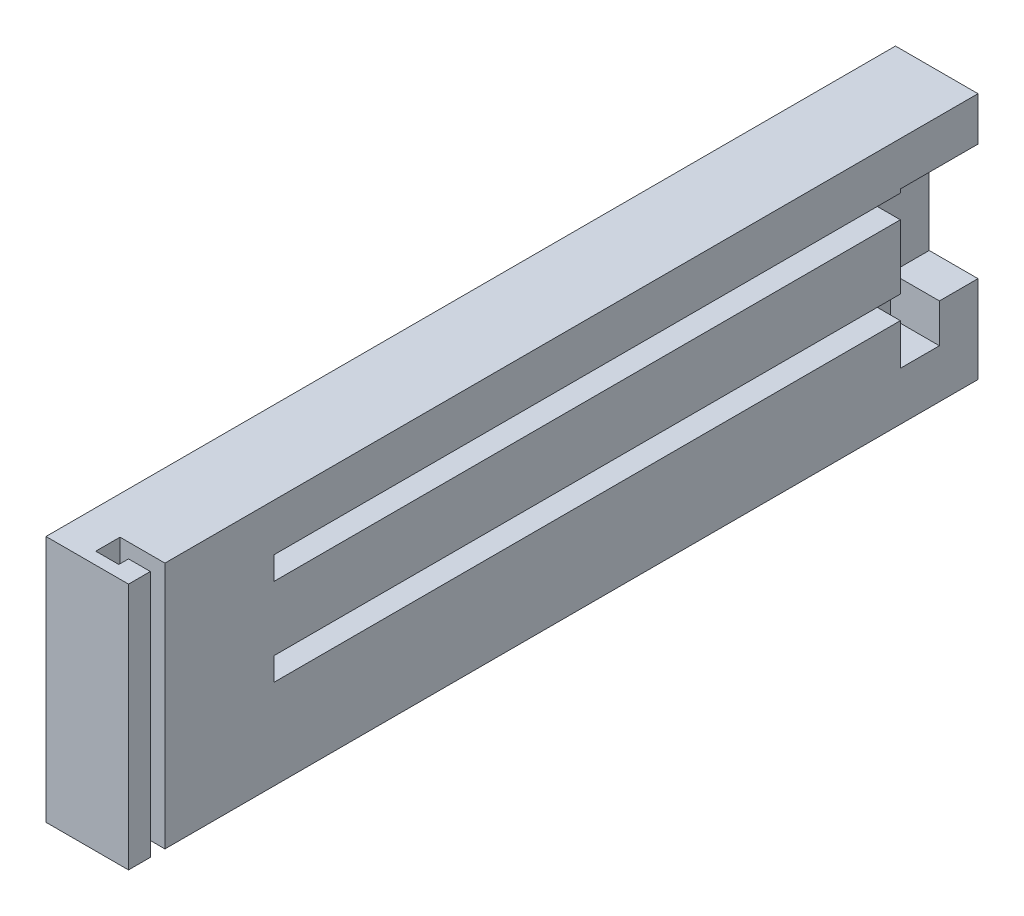
SolidWorks part; units mm, degrees
ref_plane "Front Plane" through (0, 0, 0) normal (0, 0, 1) x (1, 0, 0)
ref_plane "Top Plane" through (0, 0, 0) normal (0, 1, 0) x (1, 0, 0)
ref_plane "Right Plane" through (0, 0, 0) normal (1, 0, 0) x (0, 0, -1)
sketch "Sketch1" plane through (0, 0, 0) normal (1, 0, 0) x (0, 0, -1)
  line L1 (-64.5621, 30.5573) -> (110.4379, 30.5573)
  line L2 (-64.5621, 30.5573) -> (-64.5621, -20.4427)
  line L3 (-64.5621, -20.4427) -> (110.4379, -20.4427)
  line L4 (110.4379, 30.5573) -> (110.4379, -20.4427)
  dimension "D1" = 175
  dimension "D2" = 51
extrude "Boss-Extrude1" add sketch "Sketch1" along normal blind 17 contours L2 L3 L4 L1
sketch "Sketch6" plane through (0, 30.5573, 0) normal (0, 1, 0) x (1, 0, 0)
  line L0 (17, -64.5621) -> (17, -60.0621)
  line L1 (17, -64.5621) -> (17, 110.4379) construction
  line L2 (17, -60.0621) -> (17, -57.0621)
  line L3 (17, -57.0621) -> (14.5, -57.0621)
  line L4 (14.5, -57.0621) -> (7.75, -57.0621)
  line L5 (7.75, -57.0621) -> (7.75, -62.0621)
  line L6 (7.75, -62.0621) -> (12.5, -62.0621)
  line L7 (12.5, -62.0621) -> (12.5, -60.0621)
  line L8 (12.5, -60.0621) -> (17, -60.0621)
  line M11 (17, -64.5621) -> (17, 110.4379)
  dimension "D1" = 4.5
  dimension "D2" = 3
  dimension "D3" = 2.5
  dimension "D4" = 6.75
  dimension "D5" = 5
extrude "Cut-Extrude3" cut sketch "Sketch6" against normal through all contours L7 L8 L3 L4 L5 L6 M11
sketch "Sketch7" plane through (0, 0, -110.4379) normal (0, 0, -1) x (-1, 0, 0)
  line L0 (-17, -20.4427) -> (-17, -1.9427)
  line L1 (-17, 2.8073) -> (-17, 16.0573)
  line L2 (-12.25, 2.8073) -> (-17, 2.8073)
  line L3 (-12.25, 2.8073) -> (-12.25, -1.9427)
  line L4 (-12.25, -1.9427) -> (-17, -1.9427)
  line L5 (-17, 2.8073) -> (-17, -1.9427)
  line L6 (-17, 30.5573) -> (-17, -20.4427) construction
  line L8 (-17, 16.0573) -> (-12.25, 16.0573)
  line L9 (-17, 16.0573) -> (-17, 20.8073)
  line L10 (-17, 20.8073) -> (-12.25, 20.8073)
  line L11 (-12.25, 16.0573) -> (-12.25, 20.8073)
  line M6 (-17, 30.5573) -> (-17, -20.4427)
  dimension "D1" = 18.5
  dimension "D2" = 4.75
  dimension "D3" = 4.75
  dimension "D4" = 13.25
  dimension "D5" = 4.75
  dimension "D6" = 4.75
extrude "Cut-Extrude5" cut sketch "Sketch7" against normal blind 145 contours L4 L3 L2 M6 | L9 L8 L11 L10
sketch "Sketch10" plane through (0, 0, -110.4379) normal (0, 0, -1) x (-1, 0, 0)
  line L0 (-17, -20.4427) -> (-17, -2.4427)
  line L3 (-17, -2.4427) -> (-6.95, -2.4427)
  line L4 (-17, -2.4427) -> (-17, 21.5573)
  line L5 (-17, 21.5573) -> (-6.95, 21.5573)
  line L6 (-6.95, -2.4427) -> (-6.95, 21.5573)
  line M4 (-12.25, 2.8073) -> (-12.25, -1.9427)
  line M5 (-12.25, -1.9427) -> (-17, -1.9427)
  line M6 (-17, -1.9427) -> (-17, -20.4427)
  line M10 (-17, 30.5573) -> (-17, 20.8073)
  line M11 (-17, 2.8073) -> (-12.25, 2.8073)
  dimension "D1" = 18
  dimension "D2" = 24
  dimension "D3" = 10.05
extrude "Cut-Extrude6" cut sketch "Sketch10" against normal blind 16 contours L3 L6 L5 M10 M11 M4 M5 M6
sketch "Sketch11" plane through (0, -2.4427, 0) normal (0, 1, 0) x (1, 0, 0)
  line L0 (6.95, 94.4379) -> (6.95, 110.4379) construction
  line L1 (17, 94.4379) -> (6.95, 94.4379)
  line L2 (17, 94.4379) -> (17, 102.4879)
  line L3 (17, 102.4879) -> (6.95, 102.4879)
  line L4 (6.95, 94.4379) -> (6.95, 102.4879)
  dimension "D1" = 8.05
extrude "Cut-Extrude7" cut sketch "Sketch11" against normal blind 8
